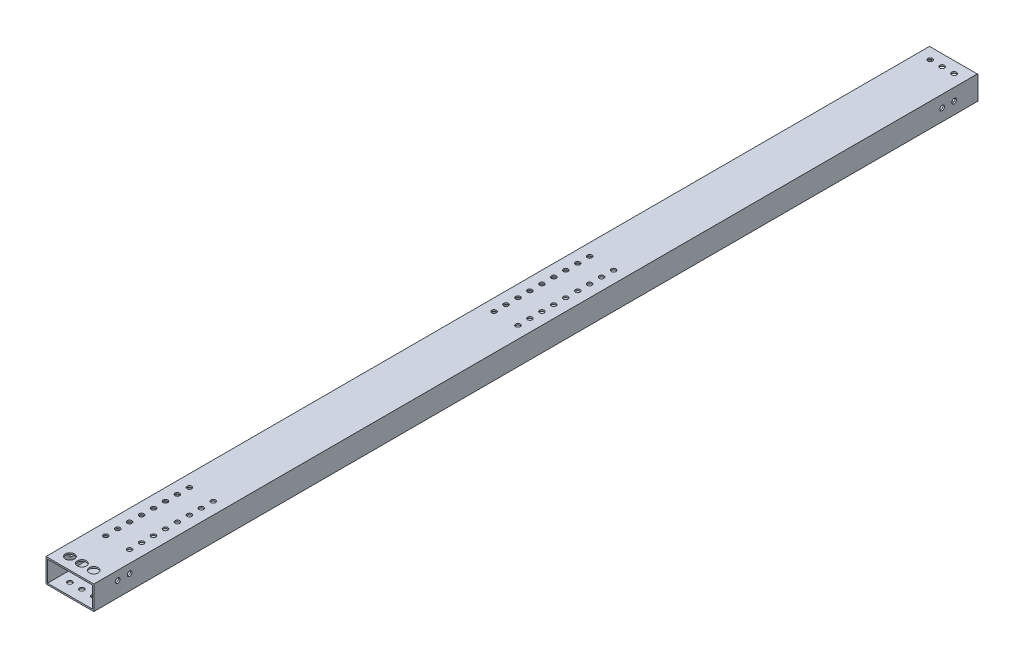
SolidWorks part; units mm, degrees
material "6061-T6 (SS)"
ref_plane "Front Plane" through (0, 0, 0) normal (0, 0, 1) x (1, 0, 0)
ref_plane "Top Plane" through (0, 0, 0) normal (0, 1, 0) x (1, 0, 0)
ref_plane "Right Plane" through (0, 0, 0) normal (1, 0, 0) x (0, 0, -1)
sketch "Sketch1" plane through (0, 0, 0) normal (0, 0, 1) x (1, 0, 0)
  line L0 (-23.8125, 11.1125) -> (23.8125, 11.1125)
  line L1 (-25.4, -12.7) -> (25.4, -12.7)
  line L2 (-25.4, -12.7) -> (-25.4, 12.7)
  line L3 (-25.4, 12.7) -> (25.4, 12.7)
  line L4 (25.4, -12.7) -> (25.4, 12.7)
  line L5 (-25.4, -12.7) -> (25.4, 12.7) construction
  line L6 (-25.4, 12.7) -> (25.4, -12.7) construction
  line L7 (23.8125, -11.1125) -> (23.8125, 11.1125)
  line L8 (-23.8125, -11.1125) -> (23.8125, -11.1125)
  line L9 (-23.8125, -11.1125) -> (-23.8125, 11.1125)
  point P0 (0, 0)
  dimension "D1" = 50.8
  dimension "D2" = 25.4
  dimension "D3" = 1.5875
extrude "Boss-Extrude1" add sketch "Sketch1" along normal mid plane 939.8
sketch "Sketch4" plane through (0, 12.7, 0) normal (0, 1, 0) x (1, 0, 0)
  line L0 (25.4, -469.9) -> (-25.4, -469.9) construction
  circle A0 centre (-12.7, -457.2) radius 4.826
  circle A1 centre (0, -457.2) radius 4.826
  circle A2 centre (12.7, -457.2) radius 4.826
  dimension "D1" = 9.652
  dimension "D2" = 12.7
  dimension "D3" = 12.7
  dimension "D4" = 12.7
extrude "Cut-Extrude3" cut sketch "Sketch4" against normal up to surface (1.5875 mm away) contours A0 | A1 | A2 up to face at (0, 11.1125, 0)
sketch "Sketch5" plane through (0, -12.7, 0) normal (0, -1, 0) x (1, 0, 0)
  circle A0 centre (-12.7, 457.2) radius 4.826 construction
  circle A1 centre (0, 457.2) radius 4.826 construction
  circle A2 centre (12.7, 457.2) radius 4.826 construction
  circle A3 centre (-12.7, 457.2) radius 4.826
  circle A4 centre (0, 457.2) radius 4.826
  circle A5 centre (12.7, 457.2) radius 4.826
  circle A6 centre (-12.7, 457.2) radius 2.5527
  circle A7 centre (0, 457.2) radius 2.5527
  circle A8 centre (12.7, 457.2) radius 2.5527
  dimension "D1" = 5.1054
extrude "Cut-Extrude4" cut sketch "Sketch5" against normal up to surface (1.5875 mm away) contours A8 | A7 | A6 up to face at (0, -11.1125, 0)
sketch "Sketch6" plane through (0, -12.7, 0) normal (0, -1, 0) x (1, 0, 0)
  line L0 (-25.4, -469.9) -> (25.4, -469.9) construction
  circle A0 centre (-12.7, -457.2) radius 2.5527
  circle A1 centre (0, -457.2) radius 2.5527
  circle A2 centre (12.7, -457.2) radius 2.5527
  dimension "D1" = 5.1054
  dimension "D2" = 12.7
  dimension "D3" = 12.7
  dimension "D4" = 12.7
extrude "Cut-Extrude5" cut sketch "Sketch6" against normal through all contours A2 | A1 | A0
sketch "Sketch7" plane through (25.4, 0, 0) normal (1, 0, 0) x (0, 0, -1)
  line L0 (-469.9, -12.7) -> (-469.9, 12.7) construction
  line L2 (469.9, -12.7) -> (469.9, 12.7) construction
  line L3 (-469.9, -12.7) -> (469.9, -12.7) construction
  circle A0 centre (-457.2, 3.175) radius 2.4892
  circle A1 centre (-444.5, 3.175) radius 2.4892
  circle A2 centre (-431.8, 3.175) radius 2.4892
  circle A3 centre (-419.1, 3.175) radius 2.4892
  circle A4 centre (457.2, 0) radius 2.5527
  circle A5 centre (444.5, 0) radius 2.5527
  circle A6 centre (431.8, 0) radius 2.5527
  dimension "D1" = 4.9784
  dimension "D7" = 5.1054
  dimension "D8" = 12.7
  dimension "D2" = 12.7
  dimension "D3" = 12.7
  dimension "D4" = 12.7
  dimension "D5" = 12.7
  dimension "D6" = 15.875
  dimension "D9" = 12.7
  dimension "D10" = 12.7
  dimension "D11" = 12.7
extrude "Cut-Extrude6" cut sketch "Sketch7" against normal through all contours A6 | A5 | A1 | A2
sketch "Sketch10" plane through (0, 12.7, 0) normal (0, 1, 0) x (1, 0, 0)
  line L1 (25.4, -469.9) -> (-25.4, -469.9) construction
  line L3 (-25.4, -469.9) -> (-25.4, 469.9) construction
  circle A0 centre (-12.7, -419.1) radius 2.4892
  circle A5 centre (12.7, -419.1) radius 2.4892
  circle A6 centre (-12.7, -406.4) radius 2.4892
  circle A7 centre (12.7, -406.4) radius 2.4892
  circle A8 centre (-12.7, -393.7) radius 2.4892
  circle A9 centre (12.7, -393.7) radius 2.4892
  circle A10 centre (-12.7, -381) radius 2.4892
  circle A11 centre (12.7, -381) radius 2.4892
  circle A12 centre (-12.7, -368.3) radius 2.4892
  circle A13 centre (12.7, -368.3) radius 2.4892
  circle A14 centre (-12.7, -355.6) radius 2.4892
  circle A15 centre (12.7, -355.6) radius 2.4892
  circle A16 centre (-12.7, -342.9) radius 2.4892
  circle A17 centre (12.7, -342.9) radius 2.4892
  circle A18 centre (-12.7, -330.2) radius 2.4892
  circle A19 centre (12.7, -330.2) radius 2.4892
  circle A20 centre (-12.7, -6.35) radius 2.4892
  circle A21 centre (12.7, -6.35) radius 2.4892
  circle A22 centre (-12.7, 6.35) radius 2.4892
  circle A23 centre (12.7, 6.35) radius 2.4892
  circle A24 centre (-12.7, 19.05) radius 2.4892
  circle A25 centre (12.7, 19.05) radius 2.4892
  circle A26 centre (-12.7, 31.75) radius 2.4892
  circle A27 centre (12.7, 31.75) radius 2.4892
  circle A28 centre (-12.7, 44.45) radius 2.4892
  circle A29 centre (12.7, 44.45) radius 2.4892
  circle A30 centre (-12.7, 57.15) radius 2.4892
  circle A31 centre (12.7, 57.15) radius 2.4892
  circle A32 centre (-12.7, 69.85) radius 2.4892
  circle A33 centre (12.7, 69.85) radius 2.4892
  circle A34 centre (-12.7, 82.55) radius 2.4892
  circle A35 centre (12.7, 82.55) radius 2.4892
  circle A36 centre (-12.7, 95.25) radius 2.4892
  circle A37 centre (12.7, 95.25) radius 2.4892
  dimension "D1" = 25.4
  dimension "D3" = 4.9784
  dimension "D2" = 12.7
  dimension "D4" = 50.8
  dimension "D5" = 12.7
  dimension "D6" = 323.85
  dimension "D8" = 12.7
  dimension "D9" = 9
extrude "Cut-Extrude8" cut sketch "Sketch10" against normal up to next (1.5875 mm away)
chamfer "Chamfer1" distance 0.762 angle 45 1 edges at (0, 12.7, -469.9)
